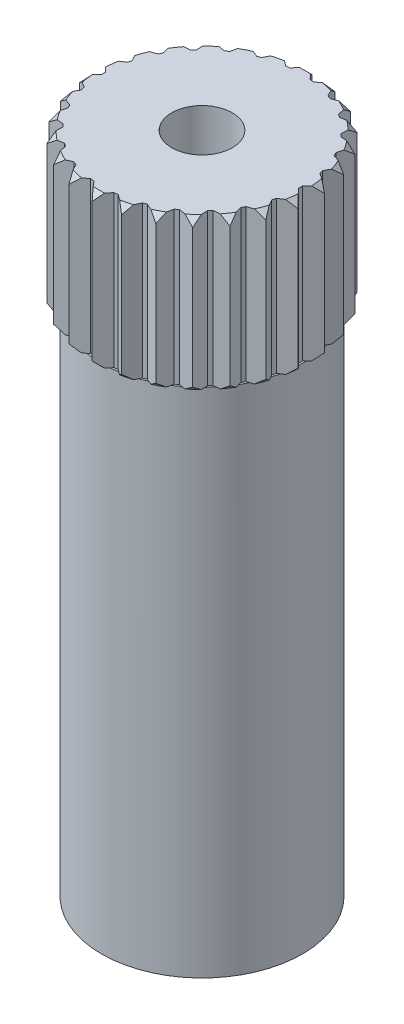
SolidWorks part; units mm, degrees
material "Brass"
ref_plane "Front Plane" through (0, 0, 0) normal (0, 0, 1) x (1, 0, 0)
ref_plane "Top Plane" through (0, 0, 0) normal (0, 1, 0) x (1, 0, 0)
ref_plane "Right Plane" through (0, 0, 0) normal (1, 0, 0) x (0, 0, -1)
sketch "ShaftS" plane through (0, 0, 0) normal (0, 1, 0) x (1, 0, 0)
  circle A0 centre (0, 0) radius 2.9
  point P2 (0, 0)
  dimension "D1" = 5.8
extrude "SHAFT" add sketch "ShaftS" along normal blind 13.5
sketch "ShaftExtensionS" plane through (0, 13.5, 0) normal (0, 1, 0) x (1, 0, 0)
  circle A0 centre (0, 0) radius 2.6
  circle A1 centre (0, 0) radius 2.9 construction
  point P2 (0, 0)
  dimension "D1" = 0.3
extrude "SHAFT EXTENSION" add sketch "ShaftExtensionS" along normal blind 4
sketch "ToothS" plane through (0, 17.5, 0) normal (0, 1, 0) x (1, 0, 0)
  line L0 (0, 2.6) -> (0, 2.9) construction
  line L1 (0, 2.9) -> (-0.2629, 2.5867)
  line L2 (0, 2.9) -> (0.2629, 2.5867)
  line L3 (-0.2629, 2.5867) -> (0.2629, 2.5867) construction
  arc A0 (0.2629, 2.5867) -> (-0.2629, 2.5867) centre (0, 0) ccw
  circle A3 centre (0, 0) radius 2.6 construction
  circle A4 centre (0, 0) radius 2.9 construction
  dimension "D1" = 80
  dimension "D2" = 0.5258
  dimension "D3" = 0.3
extrude "TOOTH" add sketch "ToothS" against normal up to body (17.5 mm away) separate body
pattern_circular "TOOTH CP" count 26 over 360 about axis through (0, 0, 0) along (0, 1, 0) of "TOOTH"
sketch "SmallBoreS" plane through (0, 17.5, 0) normal (0, 1, 0) x (1, 0, 0)
  circle A0 centre (0, 0) radius 0.8
  dimension "D1" = 1.6
extrude "SMALL BORE" cut sketch "SmallBoreS" against normal blind 4
sketch "ShaftUnderCutS" plane through (0, 0, 0) normal (0, 0, 1) x (1, 0, 0)
  line L0 (2.9, 0) -> (2.65, 0)
  line L1 (2.65, 0) -> (2.65, 13.5)
  line L2 (2.65, 13.5) -> (2.9, 13.5)
  line L3 (2.9, 13.5) -> (2.9, 0)
  line L4 (0, 0) -> (2.65, 0) construction
  line L5 (2.7115, 13.5) -> (2.3867, 13.5) construction
  line L6 (0, 13.5) -> (0, 0) construction
  point P5 (0, 0)
  point P7 (2.65, 12.2685)
  point P8 (2.8789, 13.5)
  point P10 (2.65, 13.5)
  point P13 (2.9, 0)
  dimension "D1" = 0.25
  dimension "D2" = 2.65
  dimension "D3" = 2.9
revolve "SHAFT UNDER CUT" cut sketch "ShaftUnderCutS" angle 360 about axis through (0, 13.5, 0) along (0, -1, 0)
sketch "TeethChamferS" plane through (0, 0, 0) normal (1, 0, 0) x (0, 0, -1)
  line L0 (2.9, 17.3232) -> (2.9, 17.5)
  line L1 (2.9, 17.5) -> (2.7232, 17.5)
  line L2 (2.7232, 17.5) -> (2.9, 17.3232)
  line L3 (2.9, 13.5) -> (2.9, 17.5) construction
  line L4 (2.9, 15.5) -> (0, 15.5) construction
  line L5 (0, 17.5) -> (0, 13.5) construction
  line L6 (2.7232, 13.5) -> (2.9, 13.6768)
  line L7 (2.9, 13.5) -> (2.7232, 13.5)
  line L8 (2.9, 13.6768) -> (2.9, 13.5)
  point P4 (2.9, 15.5)
  dimension "D1" = 45
  dimension "D2" = 0.25
revolve "TEETH CHAMFER" cut sketch "TeethChamferS" angle 360 about axis through (0, 13.5, 0) along (0, 1, 0)
